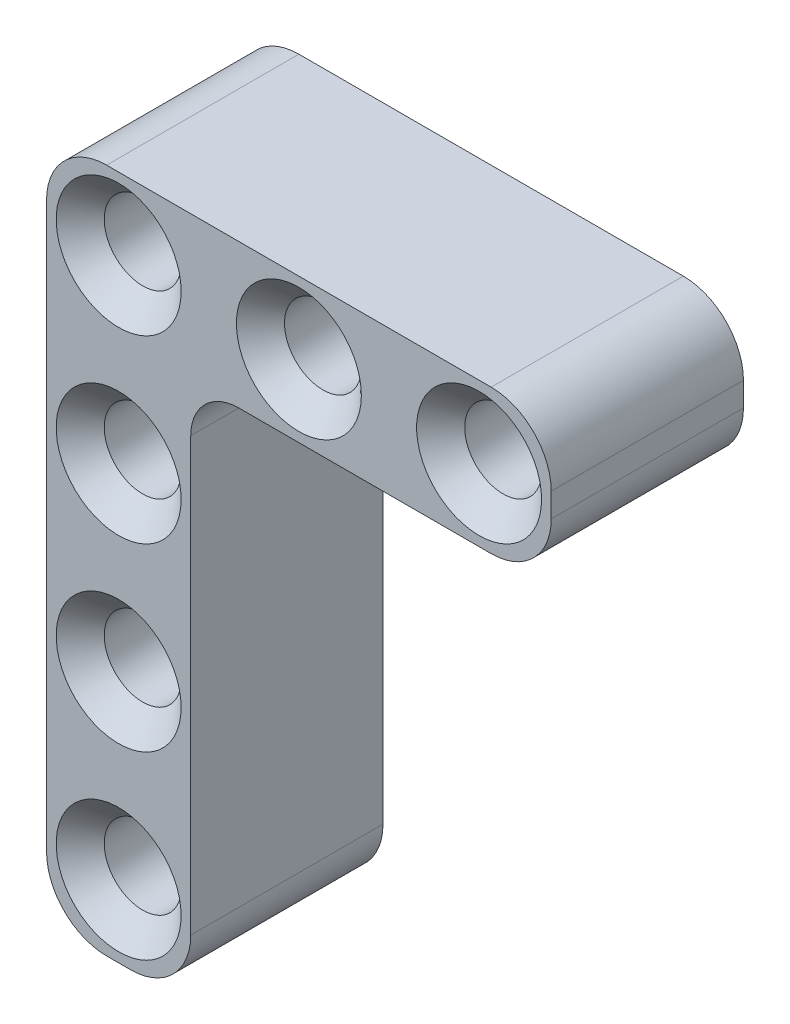
SolidWorks part; units mm, degrees
ref_plane "Front Plane" through (0, 0, 0) normal (0, 0, 1) x (1, 0, 0)
ref_plane "Top Plane" through (0, 0, 0) normal (0, 1, 0) x (1, 0, 0)
ref_plane "Right Plane" through (0, 0, 0) normal (1, 0, 0) x (0, 0, -1)
sketch "Sketch1" plane through (0, 0, 0) normal (0, 0, 1) x (1, 0, 0)
  line L1 (-0.5, 3) -> (15.5, 3)
  line L2 (-3, 0.5) -> (-3, -0.5)
  line L3 (-0.5, -3) -> (15.5, -3)
  line L4 (18, 0.5) -> (18, -0.5)
  circle A0 centre (0, 0) radius 1.6
  arc A1 (15.5, -3) -> (18, -0.5) centre (15.5, -0.5) ccw
  arc A2 (15.5, 3) -> (18, 0.5) centre (15.5, 0.5) cw
  arc A3 (-3, -0.5) -> (-0.5, -3) centre (-0.5, -0.5) ccw
  arc A4 (-0.5, 3) -> (-3, 0.5) centre (-0.5, 0.5) ccw
  circle A5 centre (7.5, 0) radius 1.6
  circle A6 centre (15, 0) radius 1.6
  point P8 (-3, 0)
  point P14 (-3, -3)
  point P17 (-3, 3)
  dimension "D1" = 3.2
  dimension "D4" = 2.5
  dimension "D2" = 6
  dimension "D3" = 3
  dimension "D6" = 7.5
  dimension "D5" = 3
extrude "Boss-Extrude1" add sketch "Sketch1" along normal blind 8
chamfer "Chamfer1" distance 1 angle 45 6 edges at (16.6, 0, 0) (16.6, 0, 8) (9.1, 0, 0) (9.1, 0, 8) (1.6, 0, 0) (1.6, 0, 8)
sketch "Sketch2" plane through (0, 0, 8) normal (0, 0, 1) x (1, 0, 0)
  line L0 (-3, 0) -> (-3, -23)
  line L1 (-0.5, -25.5) -> (0.5, -25.5)
  line L2 (3, -23) -> (3, -3)
  line L3 (-3, 0.5) -> (-3, -0.5) construction
  line L4 (-0.5, -3) -> (15.5, -3) construction
  circle A1 centre (0, -7.5) radius 1.6
  arc A4 (-3, -23) -> (-0.5, -25.5) centre (-0.5, -23) ccw
  arc A5 (0.5, -25.5) -> (3, -23) centre (0.5, -23) ccw
  circle A6 centre (0, -15) radius 1.6
  circle A7 centre (0, -22.5) radius 1.6
  point P18 (-3, -25.5)
  point P21 (3, -25.5)
  dimension "D3" = 3.2
  dimension "D8" = 2.5
  dimension "D1" = 6
  dimension "D2" = 90
  dimension "D4" = 3
  dimension "D5" = 7.5
  dimension "D7" = 3
  dimension "D6" = 3
extrude "Boss-Extrude3" add sketch "Sketch2" against normal blind 8
fillet "Fillet1" radius 2 1 edges at (3, -3, 4)
chamfer "Chamfer5" distance 1 angle 45 6 edges at (1.6, -7.5, 8) (1.6, -7.5, 0) (1.6, -15, 8) (1.6, -15, 0) (1.6, -22.5, 8) (1.6, -22.5, 0)
